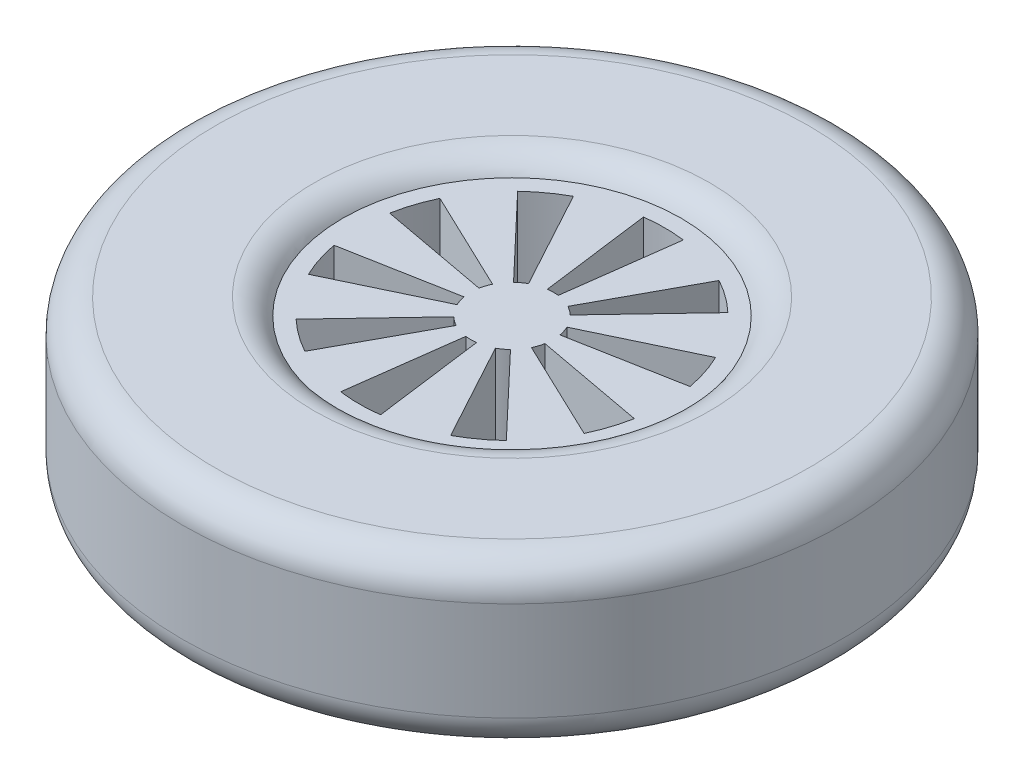
SolidWorks part; units mm, degrees
ref_plane "Front Plane" through (0, 0, 0) normal (0, 0, 1) x (1, 0, 0)
ref_plane "Top Plane" through (0, 0, 0) normal (0, 1, 0) x (1, 0, 0)
ref_plane "Right Plane" through (0, 0, 0) normal (1, 0, 0) x (0, 0, -1)
sketch "Sketch2" plane through (0, 0, 0) normal (0, 0, 1) x (1, 0, 0)
  line L0 (0, 0) -> (-75, 0) construction
  line L1 (0, 0) -> (0, 49.0199) construction
  line L3 (-100, -25) -> (-50, -25)
  line L4 (-100, -25) -> (-100, 25)
  line L5 (-100, 25) -> (-50, 25)
  line L6 (-50, -25) -> (-50, 25)
  line L7 (-100, -25) -> (-50, 25) construction
  line L8 (-100, 25) -> (-50, -25) construction
  circle A0 centre (-75, 0) radius 25 construction
  dimension "D2" = 50
  dimension "D1" = 100
revolve "Revolve1" add sketch "Sketch2" angle 360 about L1
fillet "Fillet2" radius 10 4 edges at (0, -25, -50) (0, 25, -50) (0, -25, -100) (0, 25, -100)
sketch "Sketch3" plane through (0, 0, 0) normal (0, 1, 0) x (1, 0, 0)
  circle A0 centre (0, 0) radius 50 construction
  circle A1 centre (0, 0) radius 50 construction
  circle A2 centre (0, 0) radius 60 construction
  circle A3 centre (0, 0) radius 60
extrude "Boss-Extrude2" add sketch "Sketch3" along normal blind 20 and the other way blind 20
sketch "Sketch4" plane through (0, -20, 0) normal (0, -1, 0) x (1, 0, 0)
  line L0 (0, 0) -> (0, 46.3397) construction
  line L1 (0, 0) -> (6.0486, 45.9433)
  line L2 (0, 0) -> (-6.0486, 45.9433)
  circle A1 centre (0, 0) radius 12.5
  circle A2 centre (0, 0) radius 46.3397
  circle A3 centre (0, 0) radius 46.3397
  dimension "D2" = 25
  dimension "D3" = 7.5
  dimension "D4" = 7.5
  dimension "D1" = 5
extrude "Cut-Extrude1" cut sketch "Sketch4" against normal through all contours L0 A1 L1 A3 | A1 L0 A3 L2
pattern_circular "CirPattern1" count 10 over 360 about axis through (0, 0, 0) along (0, 1, 0) of "Cut-Extrude1"
